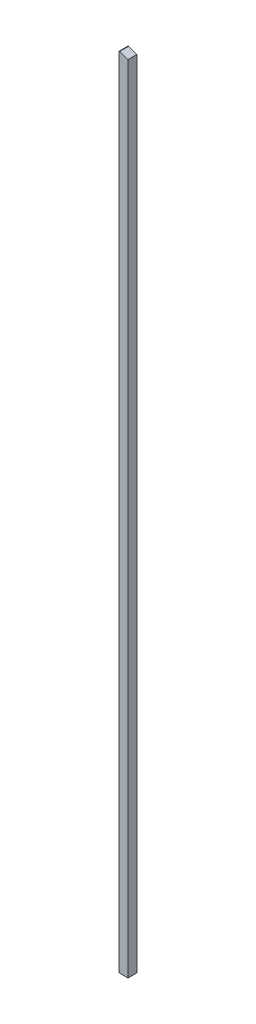
SolidWorks part; units mm, degrees
ref_plane "Front Plane" through (0, 0, 0) normal (0, 0, 1) x (1, 0, 0)
ref_plane "Top Plane" through (0, 0, 0) normal (0, 1, 0) x (1, 0, 0)
ref_plane "Right Plane" through (0, 0, 0) normal (1, 0, 0) x (0, 0, -1)
sketch "Sketch1" plane through (0, 0, 0) normal (0, 1, 0) x (1, 0, 0)
  line L1 (0, 0) -> (25.4, 0)
  line L2 (0, 0) -> (0, 25.4)
  line L3 (0, 25.4) -> (25.4, 25.4)
  line L4 (25.4, 0) -> (25.4, 25.4)
  dimension "D1" = 25.4
  dimension "D2" = 25.4
extrude "Boss-Extrude1" add sketch "Sketch1" along normal blind 2286
chamfer "Chamfer1" distance 8.382 distance2 23.876 1 edges at (25.4, 2286, -12.7)
